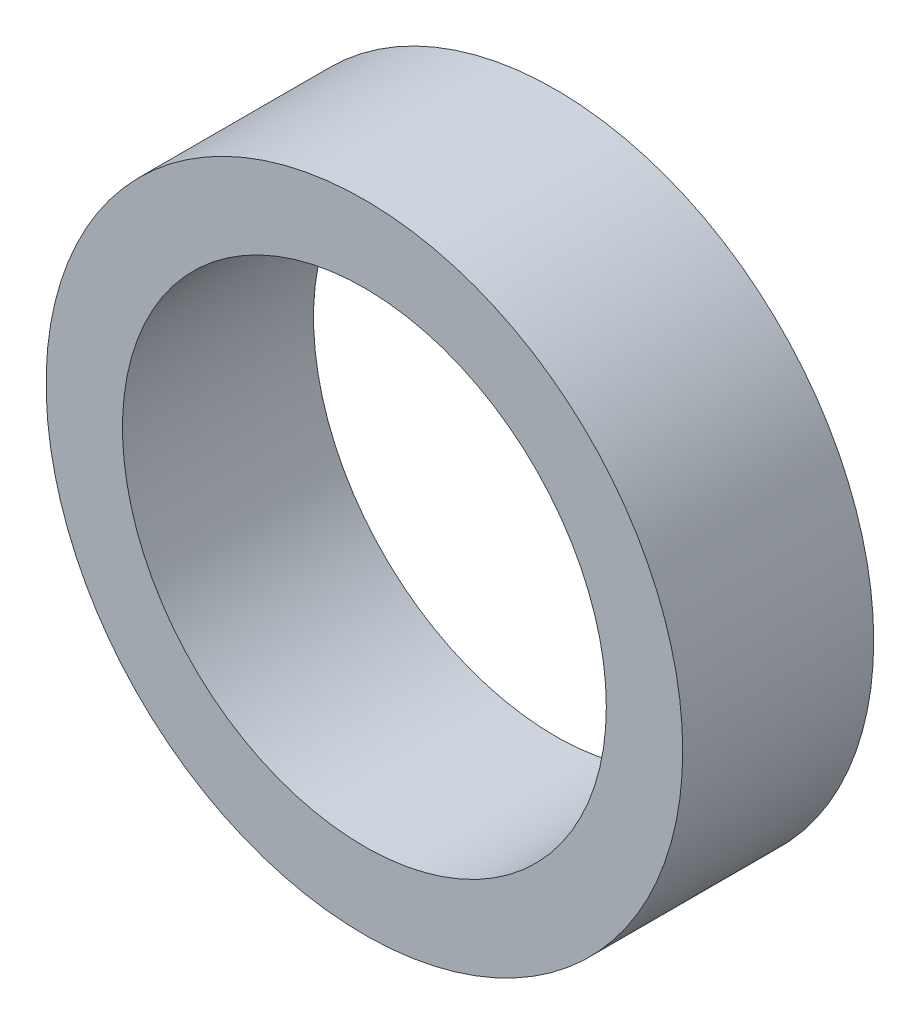
SolidWorks part; units mm, degrees
material "MDF"
ref_plane "Plano frontal" through (0, 0, 0) normal (0, 0, 1) x (1, 0, 0)
ref_plane "Plano superior" through (0, 0, 0) normal (0, 1, 0) x (1, 0, 0)
ref_plane "Plano direito" through (0, 0, 0) normal (1, 0, 0) x (0, 0, -1)
sketch "Esboço1" plane through (0, 0, 0) normal (0, 0, 1) x (1, 0, 0)
  circle A0 centre (0, 0) radius 10
  circle A1 centre (0, 0) radius 7.6
  point P8 (-7.6, 0)
  point P9 (-10, 0)
  dimension "D1" = 15.2
  dimension "D2" = 20
extrude "Ressalto-extrusão1" add sketch "Esboço1" along normal blind 6
